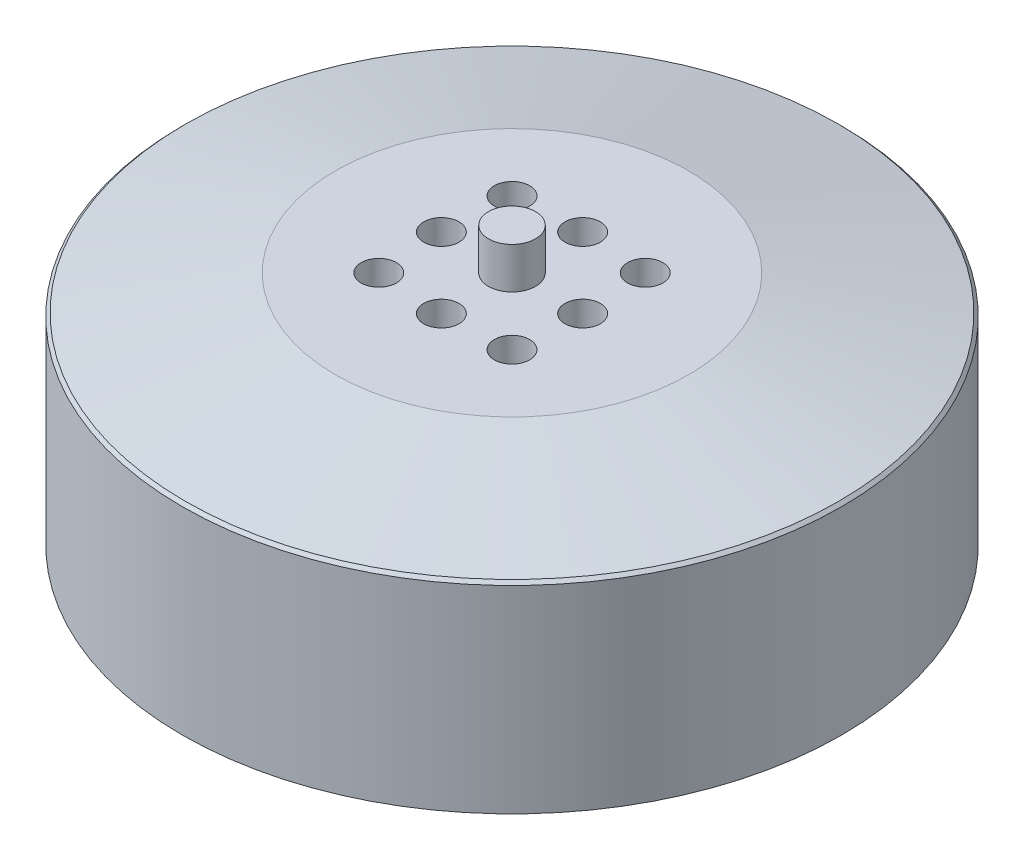
SolidWorks part; units mm, degrees
material "Alliage 1060"
ref_plane "Plan de face" through (0, 0, 0) normal (0, 0, 1) x (1, 0, 0)
ref_plane "Plan de dessus" through (0, 0, 0) normal (0, 1, 0) x (1, 0, 0)
ref_plane "Plan de droite" through (0, 0, 0) normal (1, 0, 0) x (0, 0, -1)
sketch "Esquisse1" plane through (0, 0, 0) normal (0, 1, 0) x (1, 0, 0)
  circle A0 centre (0, 0) radius 28
  dimension "D1" = 56
extrude "Boss.-Extru.1" add sketch "Esquisse1" along normal blind 20
sketch "Esquisse2" plane through (0, 0, 0) normal (1, 0, 0) x (0, 0, -1)
  line L0 (0, 20) -> (0, 0) construction
  line L1 (28, 20) -> (-28, 20) construction
  line L2 (-28, 0) -> (28, 0) construction
  line L3 (-28, 20) -> (-28, 17)
  line L4 (-28, 20) -> (-28, 0) construction
  line L5 (-28, 17) -> (-15, 20)
  line L6 (-15, 20) -> (-28, 20)
  dimension "D1" = 15
  dimension "D2" = 3
revolve "Enlèvement de matière-Révolution1" cut sketch "Esquisse2" angle 360 about L0
chamfer "Chanfrein1" distance 0.2 angle 45 1 edges at (0, 17, 28)
sketch "Esquisse3" plane through (0, 20, 0) normal (0, 1, 0) x (1, 0, 0)
  circle A0 centre (0, 0) radius 2
  dimension "D1" = 4
extrude "Boss.-Extru.2" add sketch "Esquisse3" along normal blind 3.5
sketch "Esquisse4" plane through (0, 20, 0) normal (0, 1, 0) x (1, 0, 0)
  circle A0 centre (0, 0) radius 6 construction
  circle A1 centre (0, 0) radius 7.5 construction
  circle A2 centre (0, 6) radius 1.5
  circle A3 centre (6, 0) radius 1.5
  circle A4 centre (0, -6) radius 1.5
  circle A5 centre (-6, 0) radius 1.5
  point P15 (0, 0)
  dimension "D1" = 15
  dimension "D2" = 12
  dimension "D3" = 3
  dimension "D4" = 4
extrude "Enlèv. mat.-Extru.1" cut sketch "Esquisse4" against normal blind 5
sketch "Esquisse5" plane through (0, 20, 0) normal (0, 1, 0) x (1, 0, 0)
  line L0 (0, 8) -> (0, 0) construction
  line L1 (0, 0) -> (-5.6569, 5.6569) construction
  circle A0 centre (0, 0) radius 8 construction
  circle A1 centre (-5.6569, 5.6569) radius 1.5
  circle A2 centre (5.6569, 5.6569) radius 1.5
  circle A3 centre (5.6569, -5.6569) radius 1.5
  circle A4 centre (-5.6569, -5.6569) radius 1.5
  point P15 (0, 0)
  dimension "D1" = 16
  dimension "D3" = 3
  dimension "D2" = 45
  dimension "D4" = 4
extrude "Enlèv. mat.-Extru.2" cut sketch "Esquisse5" against normal blind 10
